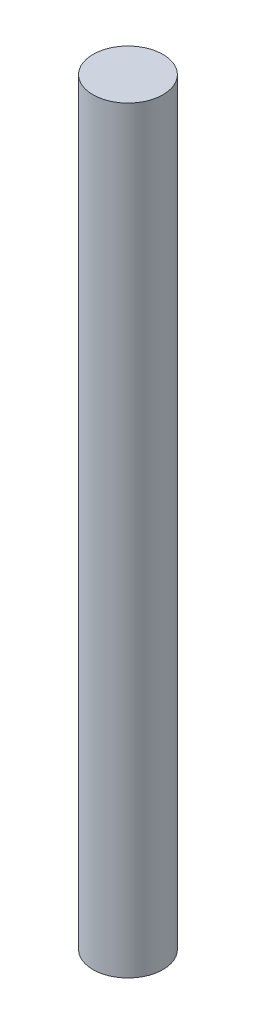
SolidWorks part; units mm, degrees
ref_plane "Front Plane" through (0, 0, 0) normal (0, 0, 1) x (1, 0, 0)
ref_plane "Top Plane" through (0, 0, 0) normal (0, 1, 0) x (1, 0, 0)
ref_plane "Right Plane" through (0, 0, 0) normal (1, 0, 0) x (0, 0, -1)
sketch "Sketch5" plane through (0, 0, 0) normal (0, 1, 0) x (1, 0, 0)
  circle A0 centre (0, 0) radius 3
  dimension "D1" = 6
extrude "Boss-Extrude3" add sketch "Sketch5" along normal blind 65
